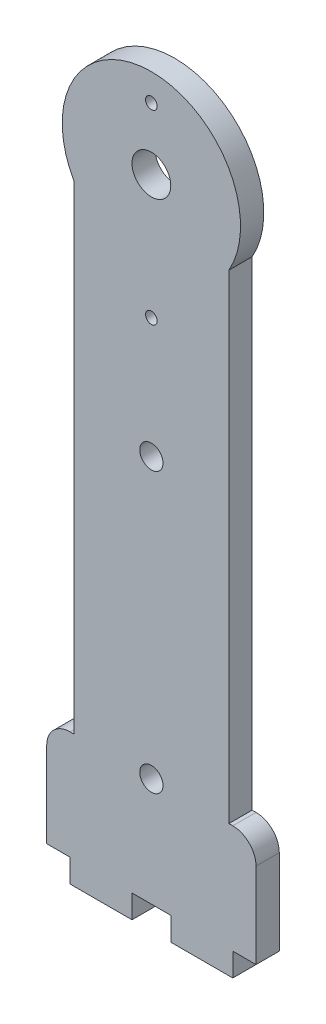
SolidWorks part; units mm, degrees
ref_plane "Alzado" through (0, 0, 0) normal (0, 0, 1) x (1, 0, 0)
ref_plane "Planta" through (0, 0, 0) normal (0, 1, 0) x (1, 0, 0)
ref_plane "Vista lateral" through (0, 0, 0) normal (1, 0, 0) x (0, 0, -1)
sketch "Croquis1" plane through (0, 0, 0) normal (0, 0, 1) x (1, 0, 0)
  line L0 (0, 0) -> (0, -104.6668) construction
  line L1 (10, 0) -> (-10, 0)
  line L2 (10, 0) -> (10, -67.5)
  line L3 (10, -67.5) -> (-10, -67.5)
  line L4 (-10, 0) -> (-10, -67.5)
  line L5 (10, 0) -> (-10, -67.5) construction
  line L6 (10, -67.5) -> (-10, 0) construction
  line L7 (13.5, -67.5) -> (-13.5, -67.5)
  line L8 (13.5, -67.5) -> (13.5, -81.5)
  line L9 (13.5, -81.5) -> (-13.5, -81.5)
  line L10 (-13.5, -67.5) -> (-13.5, -81.5)
  line L11 (13.5, -67.5) -> (-13.5, -81.5) construction
  line L12 (13.5, -81.5) -> (-13.5, -67.5) construction
  circle A0 centre (0, 0) radius 11.5
  point P3 (0, -33.75)
  point P8 (0, -74.5)
  point P16 (0, 11.5)
  dimension "D1" = 23
  dimension "D2" = 20
  dimension "D3" = 93
  dimension "D4" = 27
  dimension "D5" = 14
extrude "Saliente-Extruir1" add sketch "Croquis1" along normal blind 3 contours A0 L4 L3 L2 | L7 L10 L9 L8 L3
sketch "Croquis2" plane through (0, 0, 3) normal (0, 0, 1) x (1, 0, 0)
  line L0 (0, 0) -> (0, -81.5) construction
  line L1 (13.5, -81.5) -> (-13.5, -81.5) construction
  line L2 (13.5, -67.5) -> (10, -67.5) construction
  circle A0 centre (0, 0) radius 2.5
  circle A1 centre (0, -31.5) radius 1.5
  circle A2 centre (0, -67.5) radius 1.5
  dimension "D1" = 5
  dimension "D3" = 3
  dimension "D2" = 50
extrude "Cortar-Extruir1" cut sketch "Croquis2" against normal through all
fillet "Redondeo1" radius 3 2 edges at (-13.5, -67.5, 1.5) (13.5, -67.5, 1.5)
sketch "Croquis3" plane through (0, 0, 3) normal (0, 0, 1) x (1, 0, 0)
  line L0 (0, 0) -> (0, -16) construction
  circle A0 centre (0, -16) radius 0.75
  circle A1 centre (0, 8) radius 0.75
  dimension "D1" = 1.5
  dimension "D2" = 24
  dimension "D3" = 8
extrude "Cortar-Extruir2" cut sketch "Croquis3" against normal through all
sketch "Croquis4" plane through (0, 0, 3) normal (0, 0, 1) x (1, 0, 0)
  line L0 (13.5, -81.5) -> (-13.5, -81.5) construction
  line L1 (-10.5, -81.5) -> (-2.5, -81.5)
  line L2 (-10.5, -81.5) -> (-10.5, -84.5)
  line L3 (-10.5, -84.5) -> (-2.5, -84.5)
  line L4 (-2.5, -81.5) -> (-2.5, -84.5)
  line L5 (0, -67.5) -> (0, -81.5) construction
  line L6 (2.5, -81.5) -> (10.5, -81.5)
  line L7 (2.5, -81.5) -> (2.5, -84.5)
  line L8 (2.5, -84.5) -> (10.5, -84.5)
  line L9 (10.5, -81.5) -> (10.5, -84.5)
  line L10 (13.5, -70.5) -> (13.5, -81.5) construction
  dimension "D1" = 8
  dimension "D2" = 3
  dimension "D3" = 3
extrude "Saliente-Extruir2" add sketch "Croquis4" against normal up to vertex (3 mm away)
